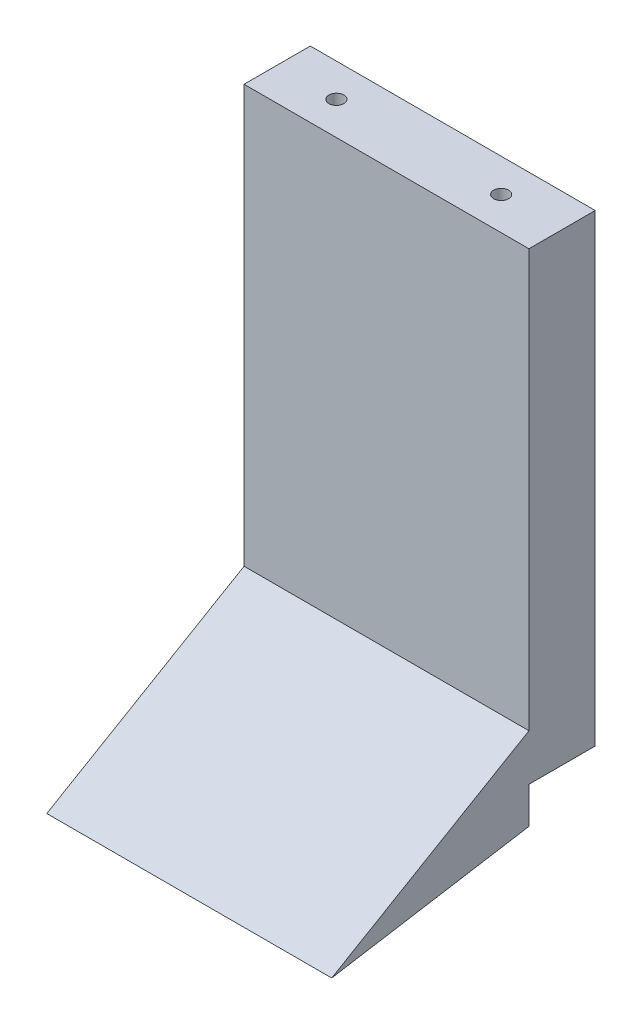
SolidWorks part; units mm, degrees
material "2024 Alloy"
ref_plane "Front Plane" through (0, 0, 0) normal (0, 0, 1) x (1, 0, 0)
ref_plane "Top Plane" through (0, 0, 0) normal (0, 1, 0) x (1, 0, 0)
ref_plane "Right Plane" through (0, 0, 0) normal (1, 0, 0) x (0, 0, -1)
sketch "Sketch1" plane through (0, 0, 0) normal (0, 1, 0) x (1, 0, 0)
  line L1 (-21.5, 5) -> (21.5, 5)
  line L2 (-21.5, 5) -> (-21.5, -5)
  line L3 (-21.5, -5) -> (21.5, -5)
  line L4 (21.5, 5) -> (21.5, -5)
  point P4 (0, 5)
  point P6 (-21.5, 0)
  dimension "D1" = 43
  dimension "D2" = 10
extrude "Boss-Extrude1" add sketch "Sketch1" along normal blind 70
sketch "Sketch2" plane through (21.5, 0, 0) normal (1, 0, 0) x (0, 0, -1)
  line L0 (-5, 7) -> (-5, -5.5)
  line L1 (-5, 70) -> (-5, 0) construction
  line L2 (-5, 7) -> (-34.7726, -10.431)
  line L3 (-34.7726, -10.431) -> (-5, -5.5)
  line L4 (-5, 0) -> (5, 0) construction
  line L6 (-34.4968, -10.4019) -> (-4.9, -5.5) construction
  dimension "D1" = 12.5
  dimension "D2" = 5.5
  dimension "D4" = 34.5
extrude "Boss-Extrude3" add sketch "Sketch2" against normal up to surface (43 mm away) contours L2 L3 L0 up to face at (-21.5, 35, 0)
sketch "Sketch3" plane through (0, 0, 0) normal (0, -1, 0) x (1, 0, 0)
  line L0 (-21.5, -5) -> (-21.5, 5) construction
  circle A0 centre (-12.515, 0) radius 0.685
  circle A1 centre (12.355, 0) radius 0.685
  dimension "D1" = 1.37
  dimension "D2" = 8.3
  dimension "D4" = 23.5
extrude "Cut-Extrude1" cut sketch "Sketch3" against normal blind 15
sketch "Sketch4" plane through (0, 70, 0) normal (0, 1, 0) x (1, 0, 0)
  line L0 (-21.5, 5) -> (-21.5, -5) construction
  circle A0 centre (-12.565, 0) radius 0.685
  circle A1 centre (12.305, 0) radius 0.685
  dimension "D1" = 1.37
  dimension "D3" = 23.5
  dimension "D2" = 8.25
extrude "Cut-Extrude2" cut sketch "Sketch4" against normal blind 15
hole_wizard "#4-40 Tapped Hole1" positions "Sketch5" profile "Sketch6" tap size "#4-40" standard "ANSI Inch"
sketch "Sketch5" plane through (0, 70, 0) normal (0, 1, 0) x (1, 0, 0)
  point P0 (12.305, 0)
  point P3 (-12.565, 0)
sketch "Sketch6" plane through (12.305, 70, 0) normal (1, 0, 0) x (0, 0, 1)
  line L0 (0, 0) -> (0, 8.2792)
  line L1 (0, 8.2792) -> (1.1303, 7.6)
  line L2 (1.1303, 7.6) -> (1.1303, 0)
  line L5 (1.1303, 0) -> (0, 0)
  line L10 (0, 8.2792) -> (-1.1303, 7.6) construction
  line L11 (0, -6.35) -> (0, 107.95) construction
  dimension "Tap Drill Dia." = 2.2606
  dimension "Tap Drill Depth" = 7.6
  dimension "Drill Angle" = 118
cosmetic thread "Hole Thread1" parameters "D1"=5.69, "D2"=2.8448
cosmetic thread "Hole Thread2" parameters "D1"=5.69, "D2"=2.8448
hole_wizard "#4-40 Tapped Hole2" positions "Sketch7" profile "Sketch8" tap size "#4-40" standard "ANSI Inch"
sketch "Sketch7" plane through (0, 0, 0) normal (0, -1, 0) x (-1, 0, 0)
  point P0 (-12.355, 0)
  point P3 (12.515, 0)
sketch "Sketch8" plane through (12.355, 0, 0) normal (1, 0, 0) x (0, 0, -1)
  line L0 (0, 0) -> (0, 8.2792)
  line L1 (0, 8.2792) -> (1.1303, 7.6)
  line L2 (1.1303, 7.6) -> (1.1303, 0)
  line L5 (1.1303, 0) -> (0, 0)
  line L10 (0, 8.2792) -> (-1.1303, 7.6) construction
  line L11 (0, -6.35) -> (0, 107.95) construction
  dimension "Tap Drill Dia." = 2.2606
  dimension "Tap Drill Depth" = 7.6
  dimension "Drill Angle" = 118
cosmetic thread "Hole Thread3" parameters "D1"=5.69, "D2"=2.8448
cosmetic thread "Hole Thread4" parameters "D1"=5.69, "D2"=2.8448
